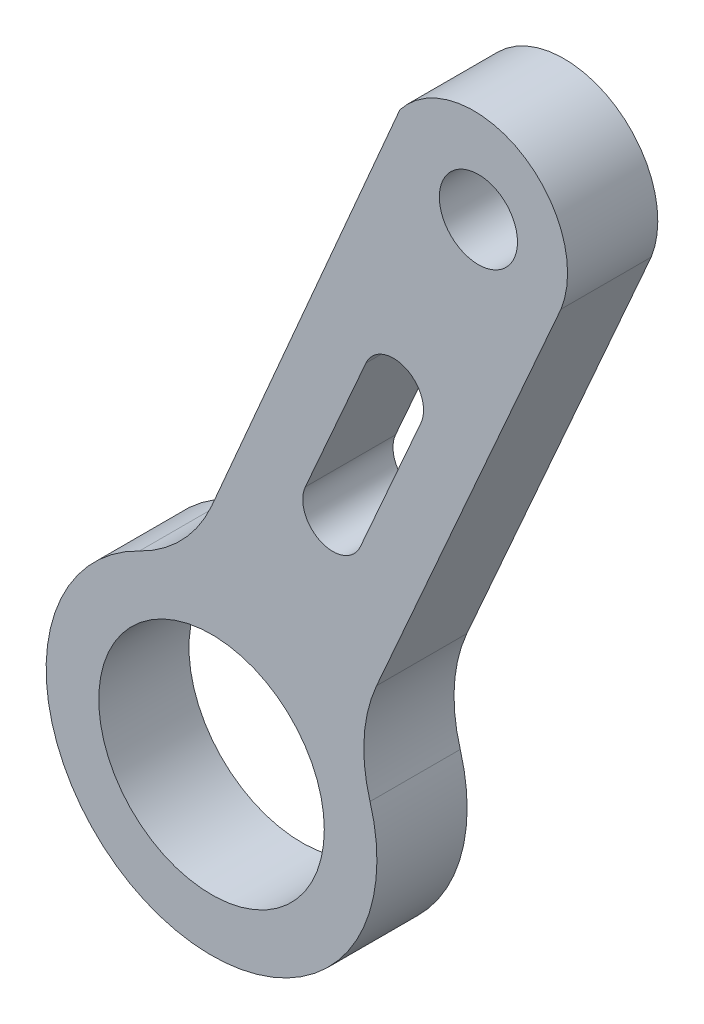
SolidWorks part; units mm, degrees
ref_plane "Front Plane" through (0, 0, 0) normal (0, 0, 1) x (1, 0, 0)
ref_plane "Top Plane" through (0, 0, 0) normal (0, 1, 0) x (1, 0, 0)
ref_plane "Right Plane" through (0, 0, 0) normal (1, 0, 0) x (0, 0, -1)
sketch "Model" plane through (0, 0, 0) normal (0, 0, 1) x (1, 0, 0)
  line L0 (59.7438, 36.5173) -> (57.7269, 31.9422)
  line L1 (57.9137, 37.3241) -> (55.8968, 32.7489)
  line L2 (64.3975, 42.1157) -> (58.2664, 28.2079)
  line L3 (59.0407, 45.1814) -> (52.7762, 30.6283)
  arc A0 (50.3805, 28.1453) -> (58.0493, 24.7646) centre (52.7779, 23.1953) ccw
  circle A1 centre (52.7779, 23.1952) radius 3.7501
  circle A2 centre (61.6524, 43.3258) radius 1.3
  arc A3 (59.7438, 36.5173) -> (57.9137, 37.3241) centre (58.8288, 36.9207) ccw
  arc A4 (55.8968, 32.7489) -> (57.7269, 31.9422) centre (56.8118, 32.3456) ccw
  arc A5 (64.3975, 42.1157) -> (59.0407, 45.1814) centre (61.5008, 43.267) ccw
  arc A6 (50.3805, 28.1453) -> (52.7762, 30.6283) centre (48.2011, 32.6452) ccw
  arc A7 (58.2664, 28.2079) -> (58.0493, 24.7646) centre (62.8414, 26.191) ccw
extrude "Boss-Extrude1" add sketch "Model" along normal blind 3
